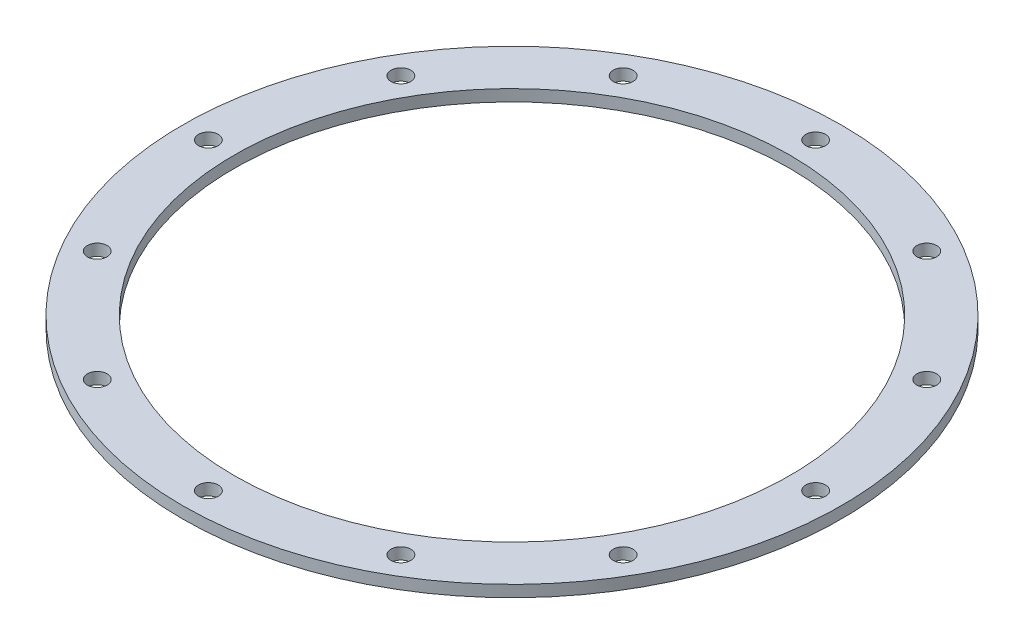
SolidWorks part; units mm, degrees
material "PTFE (general)"
ref_plane "Front Plane" through (0, 0, 0) normal (0, 0, 1) x (1, 0, 0)
ref_plane "Top Plane" through (0, 0, 0) normal (0, 1, 0) x (1, 0, 0)
ref_plane "Right Plane" through (0, 0, 0) normal (1, 0, 0) x (0, 0, -1)
ref_axis "Axis1" through (0, 55, 0) along (0, -1, 0)
sketch "Sketch1" plane through (0, 0, 0) normal (0, 0, 1) x (1, 0, 0)
  line L0 (-38.1, 0) -> (0, 0) construction
  line L1 (-38.1, 0) -> (-45.212, 0)
  line L2 (-38.1, 0) -> (-38.1, 1.5875)
  line L3 (-38.1, 1.5875) -> (-45.212, 1.5875)
  line L4 (-45.212, 0) -> (-45.212, 1.5875)
  line L7 (0, 1.5875) -> (-38.1, 1.5875) construction
  point P12 (-45.212, 0)
  point P18 (-38.1, 1.5875)
revolve "Main" add sketch "Sketch1" angle 360 about axis through (0, 55, 0) along (0, -1, 0)
sketch "Hole Location" plane through (0, 0, 0) normal (0, 1, 0) x (1, 0, 0)
  line L0 (0, 0) -> (-41.656, 0) construction
  circle A0 centre (0, 0) radius 41.656 construction
  dimension "D1" = 83.312
hole_wizard "#36 (0.1065) Diameter Hole1" positions "Sketch3" profile "Sketch5" hole size "#36" standard "ANSI Inch" end condition through all
sketch "Sketch3" plane through (0, 0, 0) normal (0, -1, 0) x (-1, 0, 0)
  point P0 (41.656, 0)
sketch "Sketch5" plane through (-41.656, 0, 0) normal (1, 0, 0) x (0, 0, -1)
  line L0 (0, 0) -> (0, 1.5875)
  line L1 (0, 1.5875) -> (1.3525, 1.5875)
  line L2 (1.3525, 1.5875) -> (1.3525, 0)
  line L5 (1.3525, 0) -> (0, 0)
  line L11 (0, -6.35) -> (0, 107.95) construction
  dimension "Thru Hole Dia." = 2.7051
  dimension "Thru Hole Depth" = 1.5875
pattern_circular "Screw Passthroughs" count 12 over 360 about axis through (0, 0, 0) along (0, 1, 0) of "#36 (0.1065) Diameter Hole1"
equation "\"D1@Hole Location\"=\"TANK DIAMETER@Cryo Tank.Assembly\"+\"GASKET SEAT THICKNESS@Cryo Tank.Assembly\""
